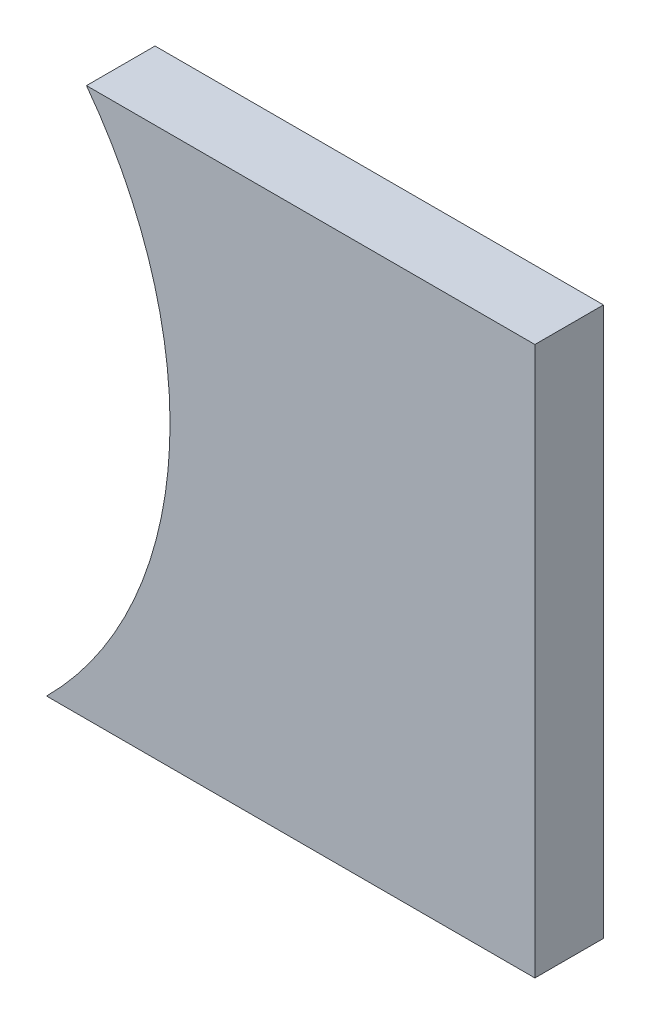
SolidWorks part; units mm, degrees
material "1.7218 (25CrMo4)"
ref_plane "Płaszczyzna XY" through (0, 0, 0) normal (0, 0, 1) x (1, 0, 0)
ref_plane "Płaszczyzna XZ" through (0, 0, 0) normal (0, 1, 0) x (1, 0, 0)
ref_plane "Płaszczyzna YZ" through (0, 0, 0) normal (1, 0, 0) x (0, 0, -1)
sketch "Szkic1" plane through (0, 0, 0) normal (0, 0, 1) x (1, 0, 0)
  line L0 (39.6607, 7.348) -> (39.9982, -8.652)
  line L4 (39.9982, -8.652) -> (67.3677, -8.652)
  line L5 (67.3677, 7.348) -> (39.6607, 7.348)
  line L6 (67.3677, -8.652) -> (67.3677, 7.348)
  line L7 (39.9982, -8.652) -> (67.3677, -8.652)
  line L8 (67.3677, 7.348) -> (39.6607, 7.348)
  line L9 (67.3677, -8.652) -> (67.3677, 7.348)
  spline S1 degree 3 poles (39.6607, 7.348) (43.565, 2.6928) (43.9042, -3.5606) (39.9982, -8.652) knots 0.687953 0.687953 0.687953 0.687953 0.866139 0.866139 0.866139 0.866139 weights 0.607906 0.497536 0.471834 0.530799
  dimension "D1" = 0
extrude "Dodanie-wyciągnięcie1" add sketch "Szkic1" against normal blind 2
sketch "Szkic2" plane through (0, 0, 0) normal (0, 0, 1) x (1, 0, 0)
  line L0 (62.3677, 7.348) -> (62.3677, -8.652)
  line L3 (67.3677, 7.348) -> (39.6607, 7.348)
  line L4 (39.9982, -8.652) -> (67.3677, -8.652)
  line L5 (67.3677, -8.652) -> (67.3677, 7.348)
  line L6 (67.3677, 7.348) -> (39.6607, 7.348)
  line L7 (39.9982, -8.652) -> (67.3677, -8.652)
  line L8 (67.3677, -8.652) -> (67.3677, 7.348)
  line L11 (39.6607, 7.348) -> (39.9982, -8.652)
  line L12 (39.6607, 7.348) -> (39.9982, -8.652)
  dimension "D2" = 5
  dimension "D1" = 0
extrude "Wytnij-wyciągnięcie1" cut sketch "Szkic2" against normal blind 5 contours L7 L8 L6 L0
sketch "Szkic3" plane through (0, 0, 0) normal (0, 0, 1) x (1, 0, 0)
  line L0 (39.6607, 7.348) -> (39.9982, -8.652)
  line L1 (39.9982, -8.652) -> (48.1252, -8.652)
  line L2 (39.9982, -8.652) -> (62.3677, -8.652) construction
  line L3 (39.6607, 7.348) -> (49.29, 7.348)
  line L4 (62.3677, 7.348) -> (39.6607, 7.348) construction
  line L5 (62.3677, 7.348) -> (62.3677, -8.652) construction
  arc A0 (48.1252, -8.652) -> (49.29, 7.348) centre (39.4885, 0.0192) ccw
  dimension "D1" = 12.2385
  dimension "D2" = 13.0777
  dimension "D3" = 14.2425
extrude "Wytnij-wyciągnięcie2" cut sketch "Szkic3" against normal blind 10
